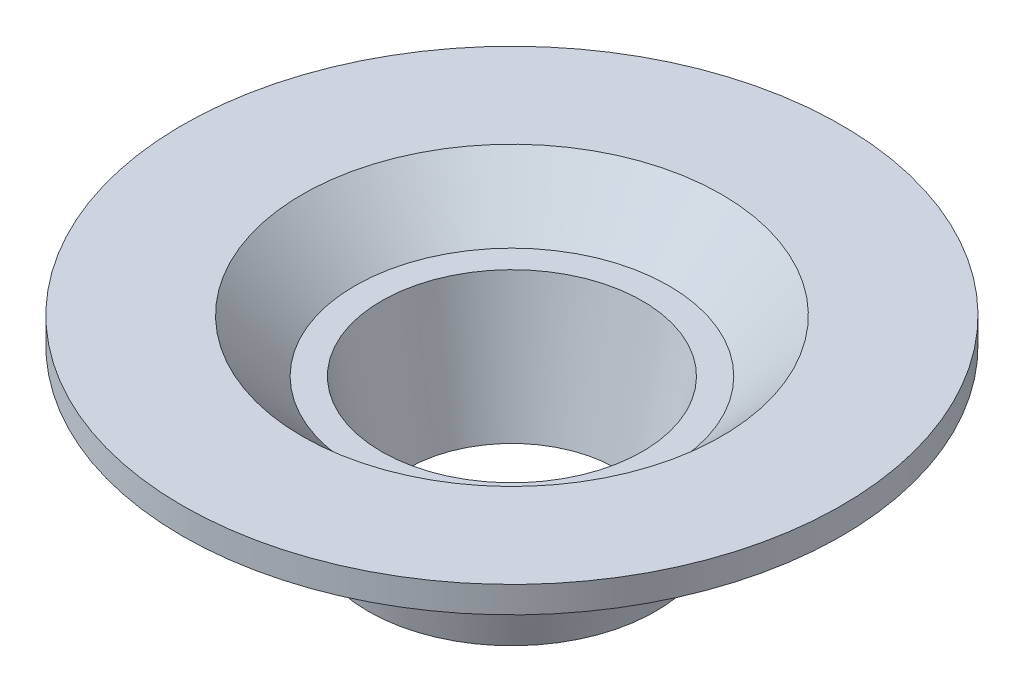
SolidWorks part; units mm, degrees
ref_plane "Front Plane" through (0, 0, 0) normal (0, 0, 1) x (1, 0, 0)
ref_plane "Top Plane" through (0, 0, 0) normal (0, 1, 0) x (1, 0, 0)
ref_plane "Right Plane" through (0, 0, 0) normal (1, 0, 0) x (0, 0, -1)
sketch "Sketch1" plane through (0, 0, 0) normal (0, 0, 1) x (1, 0, 0)
  line L0 (0, 0) -> (0, -5) construction
  line L1 (4.95, 0) -> (5.95, 0)
  line L2 (5.95, 0) -> (7.95, 2)
  line L3 (7.95, 2) -> (12.5, 2)
  line L4 (12.5, 2) -> (12.5, 1)
  line L5 (12.5, 1) -> (10.5, 1)
  line L6 (10.5, 1) -> (8.5, -1)
  line L7 (8.5, -1) -> (6.25, -1)
  line L8 (6.25, -1) -> (5.45, -5)
  line L9 (5.45, -5) -> (3.95, -5)
  line L10 (3.95, -5) -> (4.95, 0)
  dimension "D1" = 5
  dimension "D2" = 9.9
  dimension "D3" = 25
  dimension "D4" = 2
  dimension "D5" = 2
  dimension "D6" = 1
  dimension "D7" = 2
  dimension "D8" = 4
  dimension "D9" = 12.5
  dimension "D10" = 1.5
  dimension "D11" = 7.9
  dimension "D12" = 1
revolve "Revolve1" add sketch "Sketch1" angle 360 about L0
